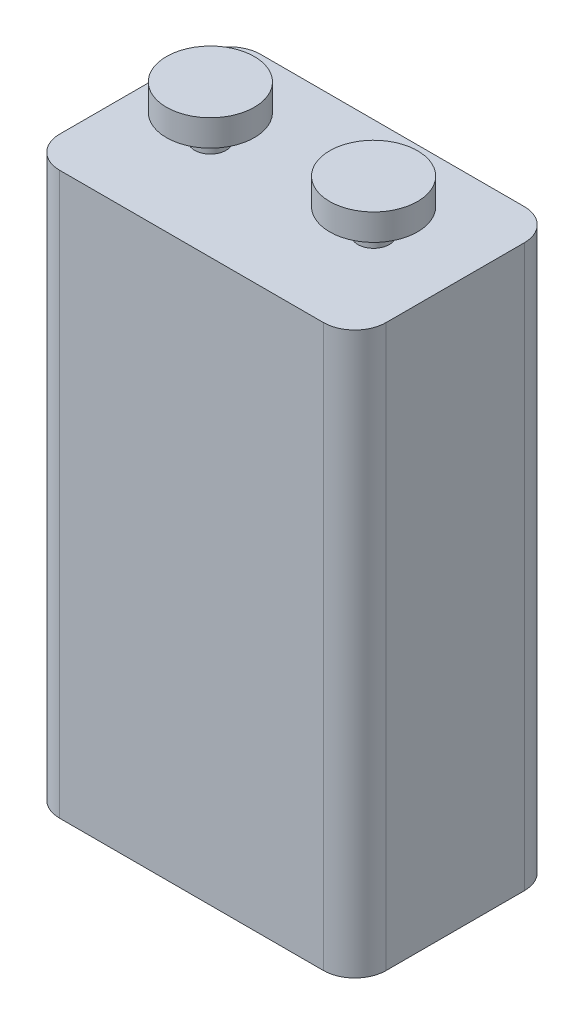
SolidWorks part; units mm, degrees
ref_plane "Front Plane" through (0, 0, 0) normal (0, 0, 1) x (1, 0, 0)
ref_plane "Top Plane" through (0, 0, 0) normal (0, 1, 0) x (1, 0, 0)
ref_plane "Right Plane" through (0, 0, 0) normal (1, 0, 0) x (0, 0, -1)
sketch "Sketch1" plane through (0, 0, 0) normal (0, 1, 0) x (1, 0, 0)
  line L1 (-10.5, 8) -> (10.5, 8)
  line L2 (-13, 5.5) -> (-13, -5.5)
  line L3 (-10.5, -8) -> (10.5, -8)
  line L4 (13, 5.5) -> (13, -5.5)
  line L5 (-13, 8) -> (13, -8) construction
  line L6 (-13, -8) -> (13, 8) construction
  arc A0 (10.5, 8) -> (13, 5.5) centre (10.5, 5.5) cw
  arc A1 (13, -5.5) -> (10.5, -8) centre (10.5, -5.5) cw
  arc A2 (-10.5, -8) -> (-13, -5.5) centre (-10.5, -5.5) cw
  arc A3 (-13, 5.5) -> (-10.5, 8) centre (-10.5, 5.5) cw
  point P0 (0, 0)
  dimension "D3" = 2.5
  dimension "D1" = 26
  dimension "D2" = 16
extrude "Boss-Extrude1" add sketch "Sketch1" along normal blind 44.7
sketch "Sketch2" plane through (0, 44.7, 0) normal (0, 1, 0) x (1, 0, 0)
  line L0 (-13, 0) -> (13, 0) construction
  line L1 (-13, 5.5) -> (-13, -5.5) construction
  line L2 (13, -5.5) -> (13, 5.5) construction
  circle A0 centre (-6.5, 0) radius 1.25
  circle A1 centre (6.5, 0) radius 1.25
  point P10 (0, 0)
  dimension "D1" = 2.5
  dimension "D2" = 2.5
  dimension "D3" = 13
  dimension "D4" = 6.5
extrude "Boss-Extrude2" add sketch "Sketch2" along normal blind 4.1
sketch "Sketch3" plane through (0, 48.8, 0) normal (0, 1, 0) x (1, 0, 0)
  circle A0 centre (-6.5, 0) radius 3.5
  circle A1 centre (6.5, 0) radius 3.5
  dimension "D1" = 7
  dimension "D2" = 7
extrude "Boss-Extrude3" add sketch "Sketch3" against normal blind 2.1
